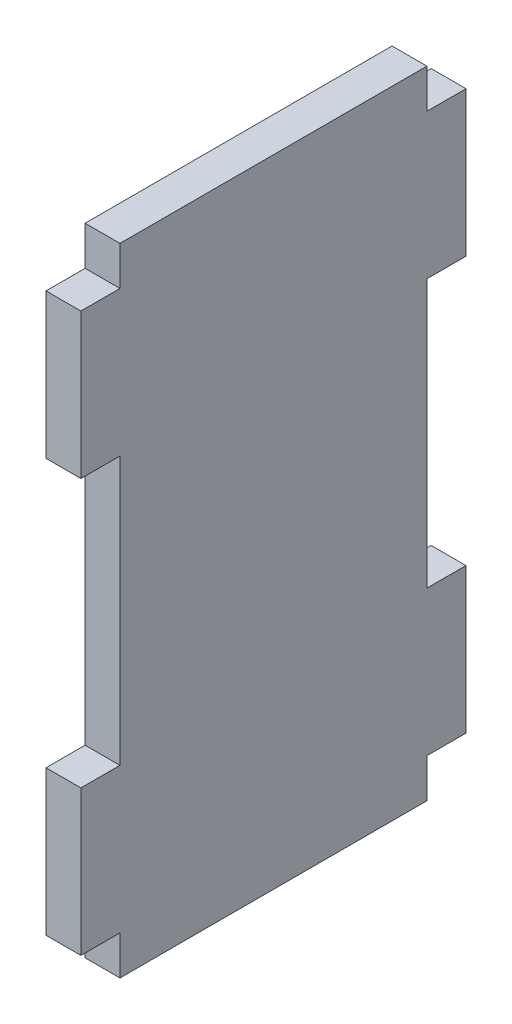
SolidWorks part; units mm, degrees
ref_plane "Front Plane" through (0, 0, 0) normal (0, 0, 1) x (1, 0, 0)
ref_plane "Top Plane" through (0, 0, 0) normal (0, 1, 0) x (1, 0, 0)
ref_plane "Right Plane" through (0, 0, 0) normal (1, 0, 0) x (0, 0, -1)
sketch "Sketch1" plane through (0, 0, 0) normal (1, 0, 0) x (0, 0, -1)
  line L1 (-261.6923, 246.5385) -> (14.3077, 246.5385)
  line L2 (-261.6923, 246.5385) -> (-261.6923, -209.4615)
  line L3 (-261.6923, -209.4615) -> (14.3077, -209.4615)
  line L4 (14.3077, 246.5385) -> (14.3077, -209.4615)
  dimension "D1" = 456
  dimension "D2" = 276
extrude "Boss-Extrude1" add sketch "Sketch1" along normal blind 25
sketch "Sketch2" plane through (0, 0, 0) normal (1, 0, 0) x (0, 0, -1)
  line L0 (-261.6923, 18.5385) -> (14.3077, 18.5385) construction
  line L1 (-261.6923, 246.5385) -> (-261.6923, -209.4615) construction
  line L2 (14.3077, -209.4615) -> (14.3077, 246.5385) construction
  line L3 (-123.6923, 246.5385) -> (-123.6923, -209.4615) construction
  line L4 (14.3077, 246.5385) -> (-261.6923, 246.5385) construction
  line L5 (-261.6923, -209.4615) -> (14.3077, -209.4615) construction
  line L6 (14.3077, -209.4615) -> (-13.6923, -209.4615)
  line L7 (-261.6923, -181.4615) -> (-233.6923, -181.4615)
  line L8 (-261.6923, -181.4615) -> (-261.6923, -209.4615)
  line L9 (-261.6923, -209.4615) -> (-233.6923, -209.4615)
  line L10 (-233.6923, -181.4615) -> (-233.6923, -209.4615)
  line L11 (14.3077, -181.4615) -> (14.3077, -209.4615)
  line L12 (14.3077, -181.4615) -> (-13.6923, -181.4615)
  line L13 (-13.6923, -181.4615) -> (-13.6923, -209.4615)
  line L14 (14.3077, 246.5385) -> (-13.6923, 246.5385)
  line L15 (14.3077, 218.5385) -> (14.3077, 246.5385)
  line L16 (14.3077, 218.5385) -> (-13.6923, 218.5385)
  line L17 (-13.6923, 218.5385) -> (-13.6923, 246.5385)
  line L18 (-261.6923, 218.5385) -> (-261.6923, 246.5385)
  line L19 (-261.6923, 218.5385) -> (-233.6923, 218.5385)
  line L20 (-261.6923, 246.5385) -> (-233.6923, 246.5385)
  line L21 (-233.6923, 218.5385) -> (-233.6923, 246.5385)
  line L22 (14.3077, -77.4615) -> (-13.6923, -77.4615)
  line L23 (-261.6923, 114.5385) -> (-233.6923, 114.5385)
  line L24 (-261.6923, 114.5385) -> (-261.6923, -77.4615)
  line L25 (-261.6923, -77.4615) -> (-233.6923, -77.4615)
  line L26 (-233.6923, 114.5385) -> (-233.6923, -77.4615)
  line L27 (14.3077, 114.5385) -> (14.3077, -77.4615)
  line L28 (14.3077, 114.5385) -> (-13.6923, 114.5385)
  line L29 (-13.6923, 114.5385) -> (-13.6923, -77.4615)
  dimension "D1" = 28
  dimension "D2" = 28
  dimension "D3" = 192
  dimension "D4" = 96
  dimension "D5" = 28
extrude "Cut-Extrude1" cut sketch "Sketch2" along normal blind 25
